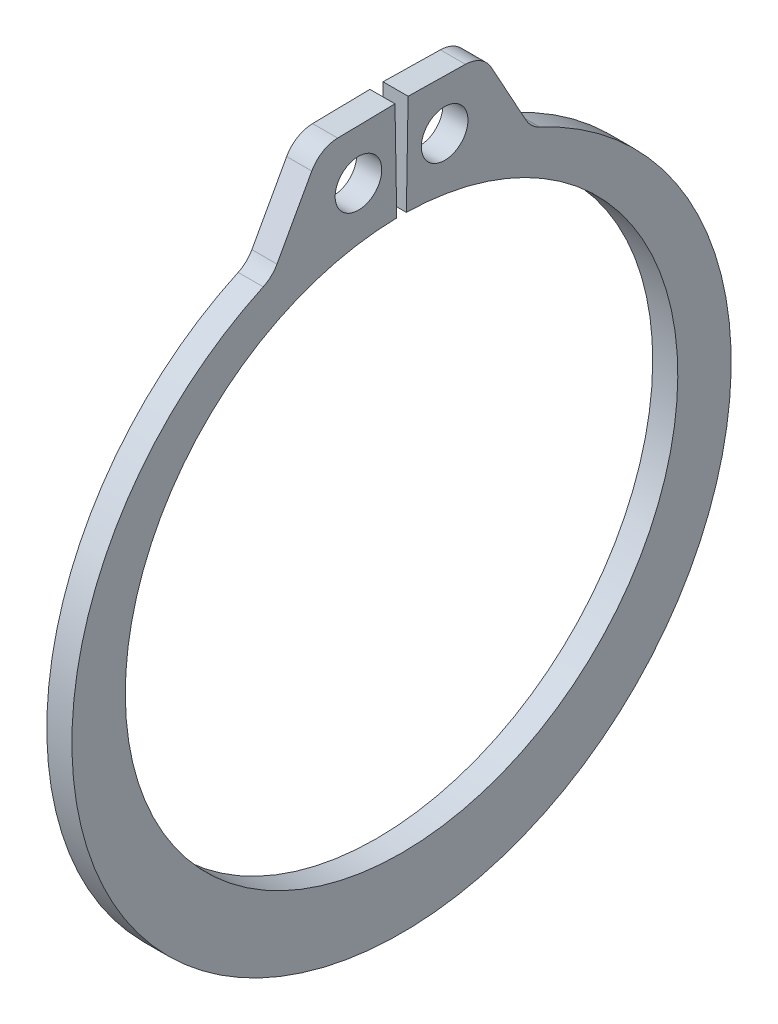
SolidWorks part; units mm, degrees
material "Cast Carbon Steel"
ref_plane "Front" through (0, 0, 0) normal (0, 0, 1) x (1, 0, 0)
ref_plane "Top" through (0, 0, 0) normal (0, 1, 0) x (1, 0, 0)
ref_plane "Right" through (0, 0, 0) normal (1, 0, 0) x (0, 0, -1)
sketch "Sketch1" plane through (0, 0, 0) normal (1, 0, 0) x (0, 0, -1)
  line L0 (0, 0) -> (0, 11.7475) construction
  line L1 (-0.205, 11.7457) -> (-0.2791, 15.9869)
  line L2 (0.2791, 15.9869) -> (3.4599, 15.9313)
  line L3 (3.4599, 15.9313) -> (5.5053, 12.2152)
  line L4 (0.205, 11.7457) -> (0.2791, 15.9869)
  line L5 (-0.2791, 15.9869) -> (-3.4599, 15.9313)
  line L6 (-3.4599, 15.9313) -> (-5.5053, 12.2152)
  line L7 (-5.5053, 12.2152) -> (-4.8269, 10.71) construction
  line L8 (5.5053, 12.2152) -> (4.8269, 10.71) construction
  line L9 (0, -11.7475) -> (0, -14.6939) construction
  line L10 (-3.4599, 15.9313) -> (-0.205, 11.7457) construction
  line L11 (0, 11.7475) -> (0, 15.9893) construction
  line L12 (-11.7475, 0) -> (11.7475, 0) construction
  circle A0 centre (0, 0) radius 11.7475 construction
  arc A1 (-0.205, 11.7457) -> (0.205, 11.7457) centre (0, 0) ccw
  circle A3 centre (0, 0) radius 17.526 construction
  circle A4 centre (-1.8325, 13.8385) radius 0.9906
  circle A5 centre (1.8325, 13.8385) radius 0.9906
  arc A6 (-5.5053, 12.2152) -> (5.5053, 12.2152) centre (0, -0.6762) ccw
  point P0 (0, -14.6939)
  dimension "A" = 23.495
  dimension "Hole" = 1.9812
  dimension "Smin" = 1.651
  dimension "H" = 4.2418
  dimension "D2" = 3.1813
  dimension "Angle" = 1
extrude "Extrude1" add sketch "Sketch1" along normal mid plane 1.0668
fillet "Fillet1" radius 1.2827 4 edges at (0, 12.2152, 5.5053) (0, 12.2152, -5.5053) (0, 15.9313, 3.4599) (0, 15.9313, -3.4599)
sketch "Sketch2" plane through (0, 0, 0) normal (0, 0, 1) x (1, 0, 0)
  line L0 (-5.9182, 0) -> (15.4178, 0)
  line L1 (15.4178, 0) -> (15.4178, -12.7)
  line L2 (-0.5842, -12.7) -> (-5.1562, -12.7)
  line L3 (15.4178, -12.7) -> (0.5842, -12.7)
  line L4 (0.5842, -12.7) -> (0.5842, -11.938)
  line L5 (0.5842, -11.938) -> (-0.5842, -11.938)
  line L6 (-0.5842, -11.938) -> (-0.5842, -12.7)
  line L7 (-0.5842, -12.7) -> (-5.9182, -12.7) construction
  line L8 (-5.9182, -12.7) -> (-5.9182, 0) construction
  line L9 (15.4178, 0) -> (76.391, 0) construction
  line L10 (-5.1562, -12.7) -> (-5.9182, -11.938)
  line L11 (-5.9182, -11.938) -> (-5.9182, 0)
  point P10 (0, -11.938)
  dimension "D2" = 21.336
  dimension "D3" = 5.334
  dimension "D1" = 45
revolve "Revolve1" [suppressed] add sketch "Sketch2" angle 360 about L9
delete or keep bodies "Body-Delete1" [suppressed] type delete bodies bodies 122
equation "\"D2@Sketch2\" = \"D1@Extrude1\"*20"
equation "\"D3@Sketch2\" = \"D2@Sketch2\"/4"
equation "\"D2@Sketch1\" = \"H@Sketch1\"*.75"
